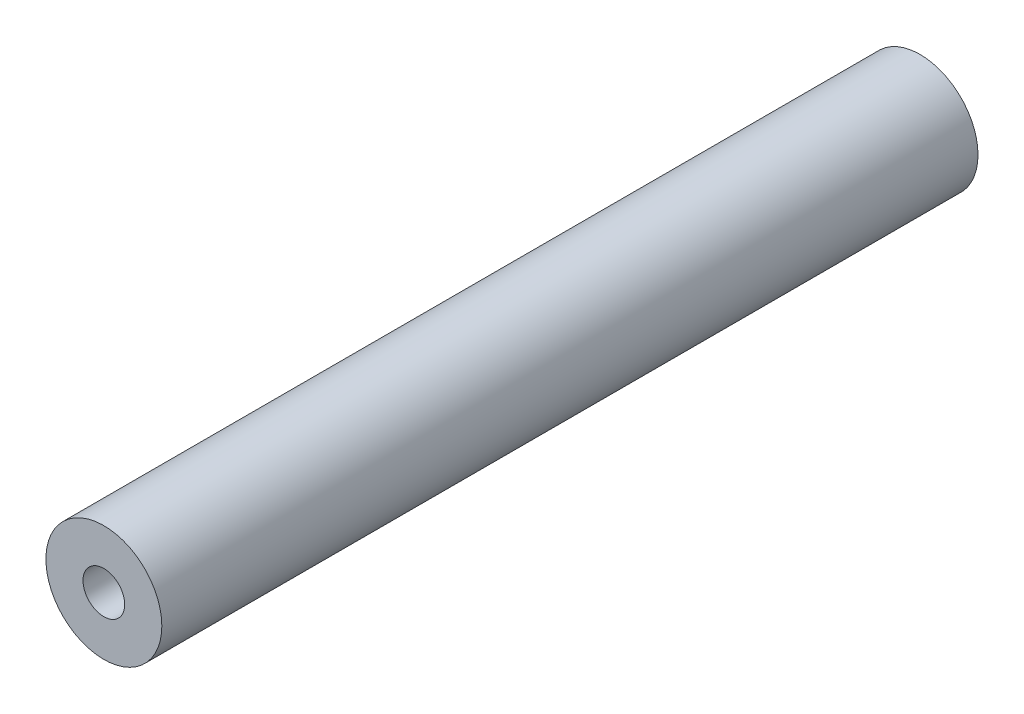
SolidWorks part; units mm, degrees
ref_plane "Front Plane" through (0, 0, 0) normal (0, 0, 1) x (1, 0, 0)
ref_plane "Top Plane" through (0, 0, 0) normal (0, 1, 0) x (1, 0, 0)
ref_plane "Right Plane" through (0, 0, 0) normal (1, 0, 0) x (0, 0, -1)
sketch "Sketch1" plane through (0, 0, 0) normal (0, 0, 1) x (1, 0, 0)
  circle A0 centre (0, 0) radius 31.75
  dimension "D1" = 63.5
extrude "Boss-Extrude1" add sketch "Sketch1" along normal blind 447.04
sketch "Sketch2" plane through (0, 0, 447.04) normal (0, 0, 1) x (1, 0, 0)
  circle A0 centre (0, 0) radius 11.43
  dimension "D1" = 22.86
extrude "Cut-Extrude1" cut sketch "Sketch2" against normal through all
